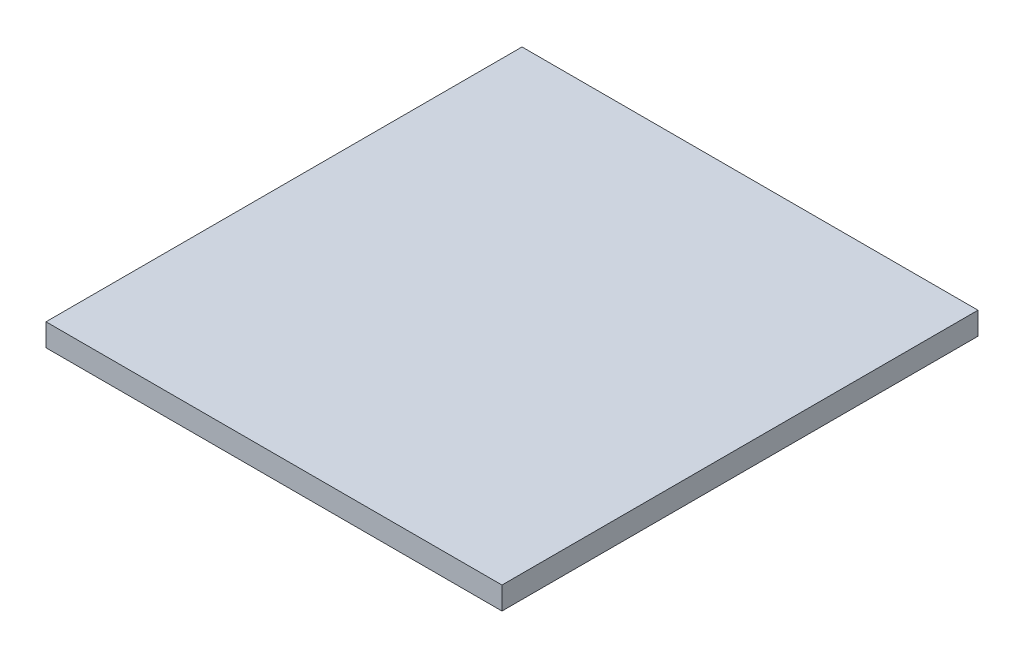
SolidWorks part; units mm, degrees
ref_plane "Front Plane" through (0, 0, 0) normal (0, 0, 1) x (1, 0, 0)
ref_plane "Top Plane" through (0, 0, 0) normal (0, 1, 0) x (1, 0, 0)
ref_plane "Right Plane" through (0, 0, 0) normal (1, 0, 0) x (0, 0, -1)
sketch "Sketch1" plane through (0, 0, 0) normal (0, 1, 0) x (1, 0, 0)
  line L1 (325.5756, -17.0557) -> (-38.4244, -17.0557)
  line L2 (325.5756, -17.0557) -> (325.5756, 362.9443)
  line L3 (325.5756, 362.9443) -> (-38.4244, 362.9443)
  line L4 (-38.4244, -17.0557) -> (-38.4244, 362.9443)
  dimension "D1" = 380
  dimension "D2" = 364
extrude "Boss-Extrude1" add sketch "Sketch1" along normal blind 18
